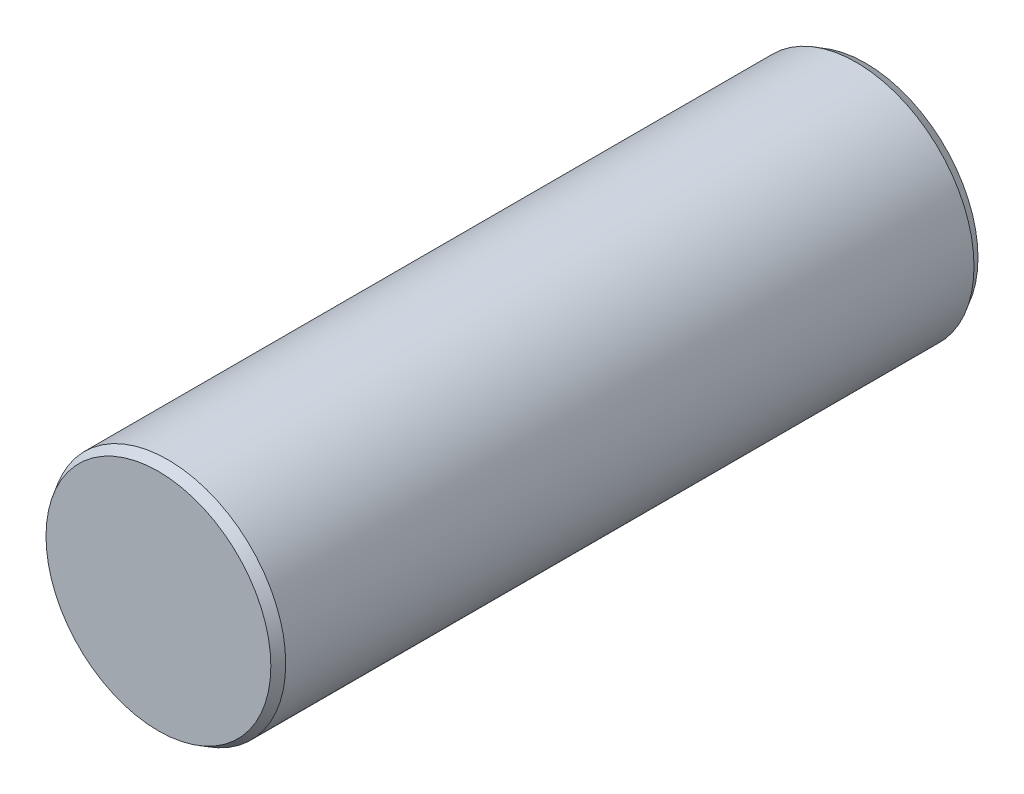
SolidWorks part; units mm, degrees
ref_plane "Plan de face" through (0, 0, 0) normal (0, 0, 1) x (1, 0, 0)
ref_plane "Plan de dessus" through (0, 0, 0) normal (0, 1, 0) x (1, 0, 0)
ref_plane "Plan de droite" through (0, 0, 0) normal (1, 0, 0) x (0, 0, -1)
sketch "Esquisse1" plane through (0, 0, 0) normal (0, 0, 1) x (1, 0, 0)
  circle A0 centre (0, 0) radius 2.5
  dimension "D1" = 5
extrude "Boss.-Extru.1" add sketch "Esquisse1" along normal mid plane 15
chamfer "Chanfrein1" distance 0.2 angle 30 2 edges at (2.5, 0, -7.5) (2.5, 0, 7.5)
